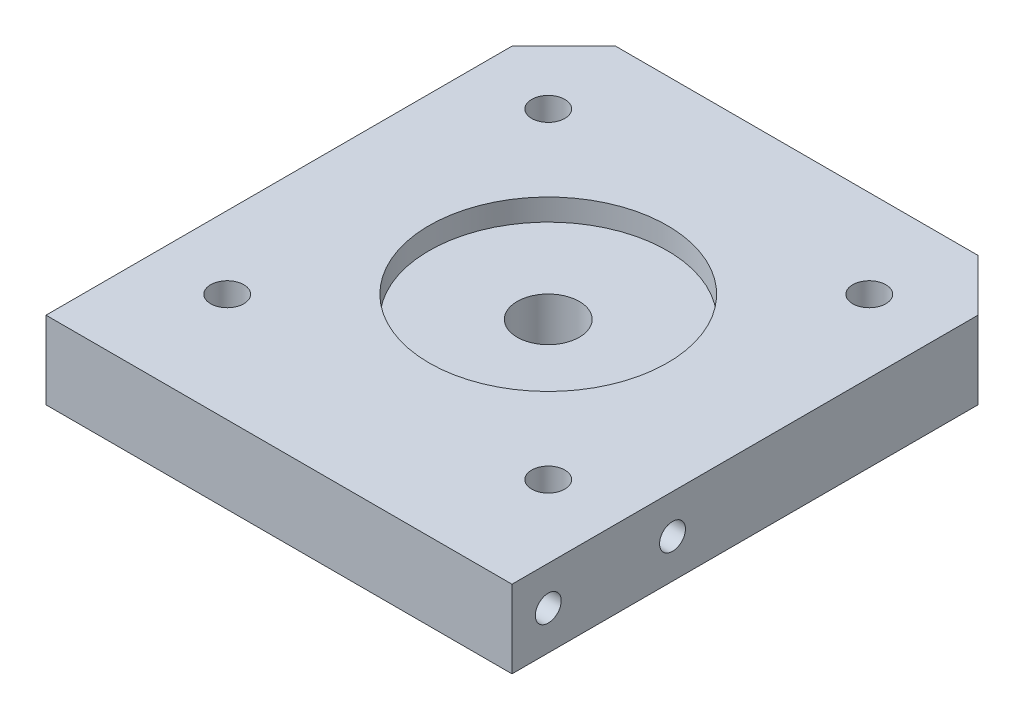
SolidWorks part; units mm, degrees
material "7075-T6 (SN)"
ref_plane "Front Plane" through (0, 0, 0) normal (0, 0, 1) x (1, 0, 0)
ref_plane "Top Plane" through (0, 0, 0) normal (0, 1, 0) x (1, 0, 0)
ref_plane "Right Plane" through (0, 0, 0) normal (1, 0, 0) x (0, 0, -1)
sketch "Sketch3" plane through (0, 0, 0) normal (0, 1, 0) x (1, 0, 0)
  line L1 (-22.5, -22.5) -> (22.5, -22.5)
  line L2 (-22.5, -22.5) -> (-22.5, 22.5)
  line L3 (-22.5, 22.5) -> (22.5, 22.5)
  line L4 (22.5, -22.5) -> (22.5, 22.5)
  line L5 (-22.5, -22.5) -> (22.5, 22.5) construction
  line L6 (-22.5, 22.5) -> (22.5, -22.5) construction
  circle A1 centre (0, -1.5) radius 3
  point P0 (0, 0)
  dimension "D2" = 6
  dimension "D1" = 45
  dimension "D3" = 1.5
extrude "Boss-Extrude2" add sketch "Sketch3" along normal blind 7.5
sketch "Sketch5" plane through (0, 7.5, 0) normal (0, 1, 0) x (1, 0, 0)
  circle A0 centre (0, -1.5) radius 11.5
  circle A1 centre (0, -1.5) radius 3 construction
  dimension "D1" = 23
extrude "Cut-Extrude1" cut sketch "Sketch5" against normal blind 2.1
chamfer "Chamfer1" distance 5 angle 45 2 edges at (22.5, 3.75, -22.5) (-22.5, 3.75, -22.5)
hole_wizard "CBORE for M3 Hex Socket Head Cap Screw1" positions "Sketch8" profile "Sketch9" counterbore size "M3" standard "DIN" end condition up to next
sketch "Sketch8" plane through (0, 0, 0) normal (0, -1, 0) x (-1, 0, 0)
  line L1 (-15.5, -17) -> (15.5, -17) construction
  line L2 (-15.5, -17) -> (-15.5, 14) construction
  line L3 (-15.5, 14) -> (15.5, 14) construction
  line L4 (15.5, -17) -> (15.5, 14) construction
  line L7 (15.5, 14) -> (-15.5, -17) construction
  line L9 (15.5, -17) -> (-15.5, 14) construction
  line L10 (0, -1.5) -> (0, 0) construction
  point P2 (15.5, 14)
  point P41 (-15.5, -17)
  point P42 (-15.5, 14)
  point P43 (15.5, -17)
  dimension "D1" = 31
  dimension "D2" = 1.5
sketch "Sketch9" plane through (-15.5, 0, -14) normal (1, 0, 0) x (0, 0, -1)
  line L0 (0, 0) -> (0, 7.5)
  line L1 (0, 7.5) -> (1.6, 7.5)
  line L3 (1.6, 7.5) -> (1.6, 3.5)
  line L4 (1.6, 3.5) -> (3.25, 3.5)
  line L5 (3.25, 3.5) -> (3.25, 0)
  line L7 (3.25, 0) -> (0, 0)
  line L11 (0, -6.35) -> (0, 107.95) construction
  dimension "Thru Hole Dia." = 3.2
  dimension "Thru Hole Depth" = 7.5
  dimension "C'Bore Dia." = 6.5
  dimension "C'Bore Depth" = 3.5
sketch "Sketch10" plane through (0, 0, 22.5) normal (0, 0, 1) x (1, 0, 0)
  line L1 (-22.5, 7.5) -> (22.5, 7.5)
  line L2 (-22.5, 7.5) -> (-22.5, 0)
  line L3 (-22.5, 0) -> (22.5, 0)
  line L4 (22.5, 7.5) -> (22.5, 0)
extrude "Boss-Extrude3" add sketch "Sketch10" along normal blind 5
hole_wizard "M3 Tapped Hole2" positions "Sketch13" profile "Sketch14" tap size "M3" standard "DIN"
sketch "Sketch13" plane through (-22.5, 0, 0) normal (-1, 0, 0) x (0, 0, 1)
  line L0 (-17.5, 0) -> (27.5, 0) construction
  line L2 (15.5, 7.5) -> (15.5, 0) construction
  line L3 (-17.5, 7.5) -> (27.5, 7.5) construction
  line L5 (27.5, 7.5) -> (27.5, 0) construction
  point P0 (24, 3.75)
  point P2 (12, 3.75)
  dimension "D1" = 12
  dimension "D2" = 8.5
  dimension "D3" = 3.5
  dimension "D4" = 3.75
sketch "Sketch14" plane through (-22.5, 3.75, 24) normal (0, 1, 0) x (0, 0, 1)
  line L0 (0, 0) -> (0, 10.7511)
  line L1 (0, 10.7511) -> (1.25, 10)
  line L2 (1.25, 10) -> (1.25, 0)
  line L5 (1.25, 0) -> (0, 0)
  line L10 (0, 10.7511) -> (-1.25, 10) construction
  line L11 (0, -6.35) -> (0, 107.95) construction
  dimension "Tap Drill Dia." = 2.5
  dimension "Tap Drill Depth" = 10
  dimension "Drill Angle" = 118
cosmetic thread "Hole Thread5" parameters "D1"=7.5, "D2"=3
cosmetic thread "Hole Thread6" parameters "D1"=7.5, "D2"=3
mirror "Mirror1" about plane through (0, 0, 0) normal (1, 0, 0) of "M3 Tapped Hole2"
